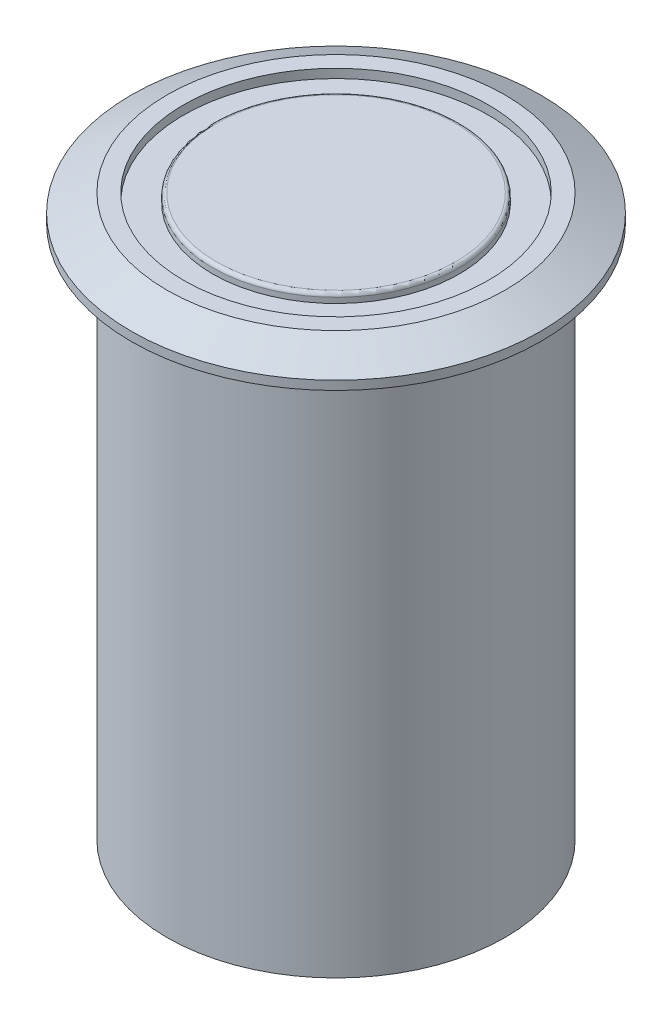
SolidWorks part; units mm, degrees
ref_plane "前视" through (0, 0, 0) normal (0, 0, 1) x (1, 0, 0)
ref_plane "上视" through (0, 0, 0) normal (0, 1, 0) x (1, 0, 0)
ref_plane "右视" through (0, 0, 0) normal (1, 0, 0) x (0, 0, -1)
sketch "草图1" plane through (0, 0, 0) normal (0, 1, 0) x (1, 0, 0)
  circle A0 centre (0, 0) radius 9.5
  dimension "D1" = 19
extrude "凸台-拉伸1" add sketch "草图1" along normal blind 30
sketch "草图2" plane through (0, 30, 0) normal (0, 1, 0) x (1, 0, 0)
  circle A0 centre (0, 0) radius 11.5
  dimension "D1" = 23
extrude "凸台-拉伸2" add sketch "草图2" along normal blind 1.5
chamfer "倒角1" distance 1 distance2 2 1 edges at (0, 31.5, 11.5)
sketch "草图3" plane through (0, 31.5, 0) normal (0, 1, 0) x (1, 0, 0)
  circle A0 centre (0, 0) radius 8.5535
  circle A1 centre (0, 0) radius 6.9291
extrude "切除-拉伸1" cut sketch "草图3" against normal blind 0.5
fillet "圆角1" radius 0.2 1 edges at (0, 31.5, 6.9291)
